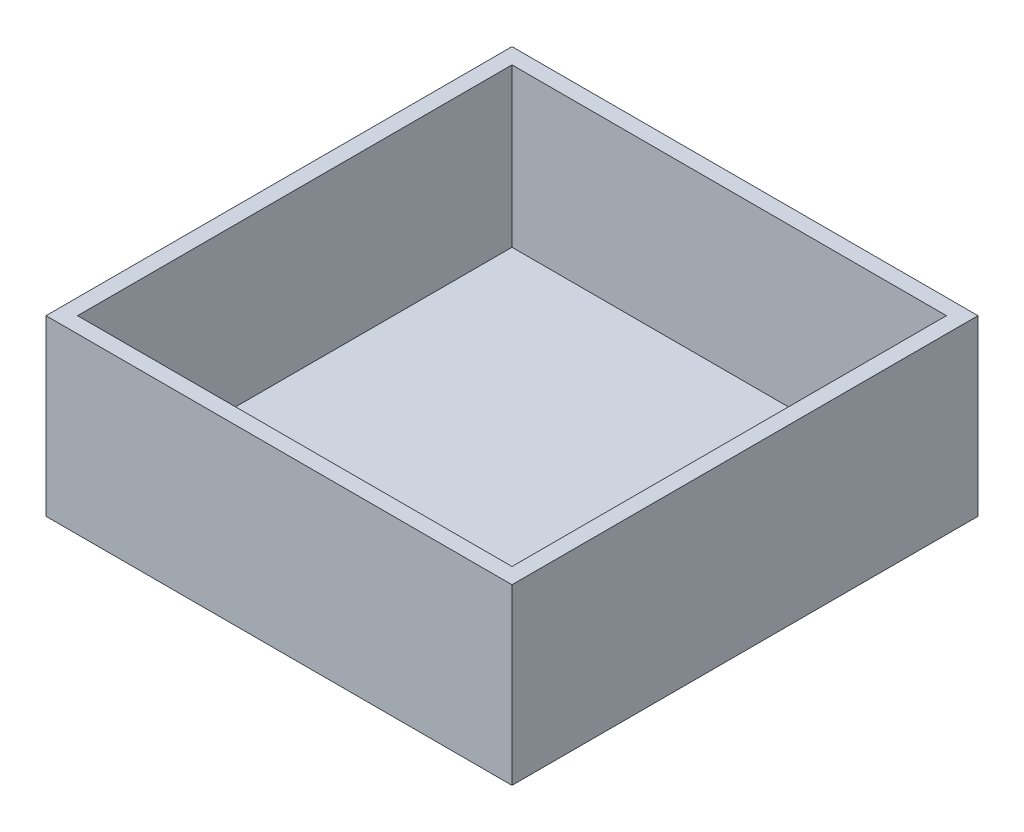
SolidWorks part; units mm, degrees
ref_plane "Front Plane" through (0, 0, 0) normal (0, 0, 1) x (1, 0, 0)
ref_plane "Top Plane" through (0, 0, 0) normal (0, 1, 0) x (1, 0, 0)
ref_plane "Right Plane" through (0, 0, 0) normal (1, 0, 0) x (0, 0, -1)
sketch "Sketch1" plane through (0, 0, 0) normal (0, 1, 0) x (1, 0, 0)
  line L1 (0, 0) -> (59, 0)
  line L2 (0, 0) -> (0, -59)
  line L3 (0, -59) -> (59, -59)
  line L4 (59, 0) -> (59, -59)
  line L5 (2, -2) -> (57, -2)
  line L6 (2, -2) -> (2, -57)
  line L7 (2, -57) -> (57, -57)
  line L8 (57, -2) -> (57, -57)
  dimension "D1" = 59
  dimension "D2" = 59
  dimension "D3" = 2
  dimension "D4" = 2
  dimension "D5" = 2
  dimension "D6" = 2
extrude "Boss-Extrude1" add sketch "Sketch1" along normal blind 20
sketch "Sketch2" plane through (0, 0, 0) normal (0, -1, 0) x (1, 0, 0)
  line L1 (0, 0) -> (59, 0)
  line L2 (0, 0) -> (0, 59)
  line L3 (0, 59) -> (59, 59)
  line L4 (59, 0) -> (59, 59)
extrude "Boss-Extrude2" add sketch "Sketch2" along normal blind 2
